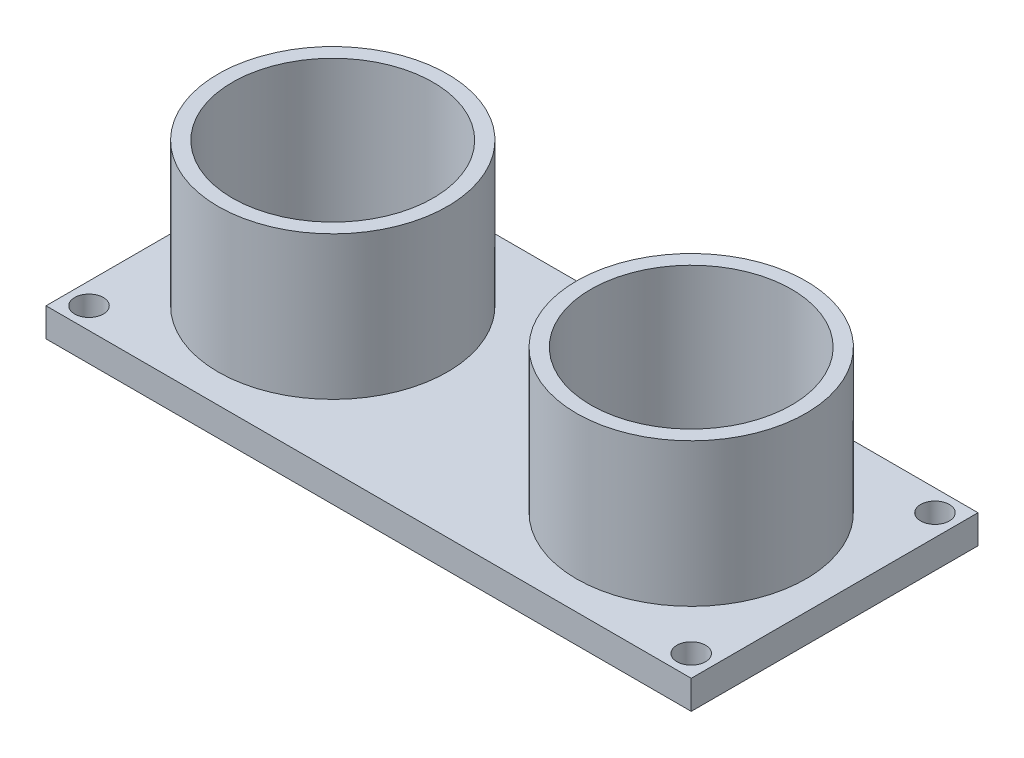
SolidWorks part; units mm, degrees
ref_plane "Front Plane" through (0, 0, 0) normal (0, 0, 1) x (1, 0, 0)
ref_plane "Top Plane" through (0, 0, 0) normal (0, 1, 0) x (1, 0, 0)
ref_plane "Right Plane" through (0, 0, 0) normal (1, 0, 0) x (0, 0, -1)
sketch "Sketch1" plane through (0, 0, 0) normal (0, 1, 0) x (1, 0, 0)
  line L0 (-27.3496, 0) -> (27.3496, 0) construction
  line L1 (-22.5, -10) -> (22.5, -10)
  line L2 (-22.5, -10) -> (-22.5, 10)
  line L3 (-22.5, 10) -> (22.5, 10)
  line L4 (22.5, -10) -> (22.5, 10)
  line L5 (0, -14.4399) -> (0, 14.4399) construction
  circle A0 centre (-12.5, 0) radius 8
  circle A1 centre (-12.5, 0) radius 7
  circle A2 centre (-21, 8.5) radius 1
  circle A3 centre (-21, -8.5) radius 1
  circle A4 centre (21, -8.5) radius 1
  circle A5 centre (21, 8.5) radius 1
  circle A6 centre (12.5, 0) radius 7
  circle A7 centre (12.5, 0) radius 8
  point P0 (0, 0)
  point P15 (0, 0)
  point P17 (0, 0)
  dimension "D4" = 16
  dimension "D5" = 14
  dimension "D6" = 2
  dimension "D7" = 1.5
  dimension "D1" = 20
  dimension "D2" = 45
  dimension "D3" = 10
  dimension "D8" = 1.5
extrude "Boss-Extrude1" add sketch "Sketch1" along normal blind 2 contours L1 L4 L3 L2 A3 A2 A0 A4 A5 A7 | A1 | A0 A1 | A6 | A7 A6
sketch "Sketch2" plane through (0, 0, 0) normal (0, 1, 0) x (1, 0, 0)
  line L4 (-22.5, -10) -> (22.5, -10)
  line L5 (22.5, -10) -> (22.5, 10)
  line L6 (22.5, 10) -> (-22.5, 10)
  line L7 (-22.5, 10) -> (-22.5, -10)
  line L8 (-22.5, -10) -> (22.5, -10)
  line L9 (22.5, -10) -> (22.5, 10)
  line L10 (22.5, 10) -> (-22.5, 10)
  line L11 (-22.5, 10) -> (-22.5, -10)
  circle A1 centre (-21, 8.5) radius 1
  circle A2 centre (-21, 8.5) radius 1
  circle A3 centre (-12.5, 0) radius 7
  circle A4 centre (-12.5, 0) radius 7
  circle A5 centre (-12.5, 0) radius 8
  circle A6 centre (-12.5, 0) radius 8
  circle A7 centre (12.5, 0) radius 8
  circle A8 centre (12.5, 0) radius 8
  circle A9 centre (12.5, 0) radius 7
  circle A10 centre (12.5, 0) radius 7
  circle A11 centre (21, 8.5) radius 1
  circle A12 centre (21, 8.5) radius 1
  circle A13 centre (21, -8.5) radius 1
  circle A14 centre (21, -8.5) radius 1
  circle A15 centre (-21, -8.5) radius 1
  circle A16 centre (-21, -8.5) radius 1
  dimension "D1" = 0
  dimension "D2" = 0
  dimension "D3" = 0
  dimension "D4" = 0
  dimension "D5" = 0
  dimension "D6" = 0
  dimension "D7" = 0
  dimension "D8" = 0
  dimension "D9" = 0
extrude "Boss-Extrude2" add sketch "Sketch2" along normal blind 12 contours A6 A4 | A8 A10
